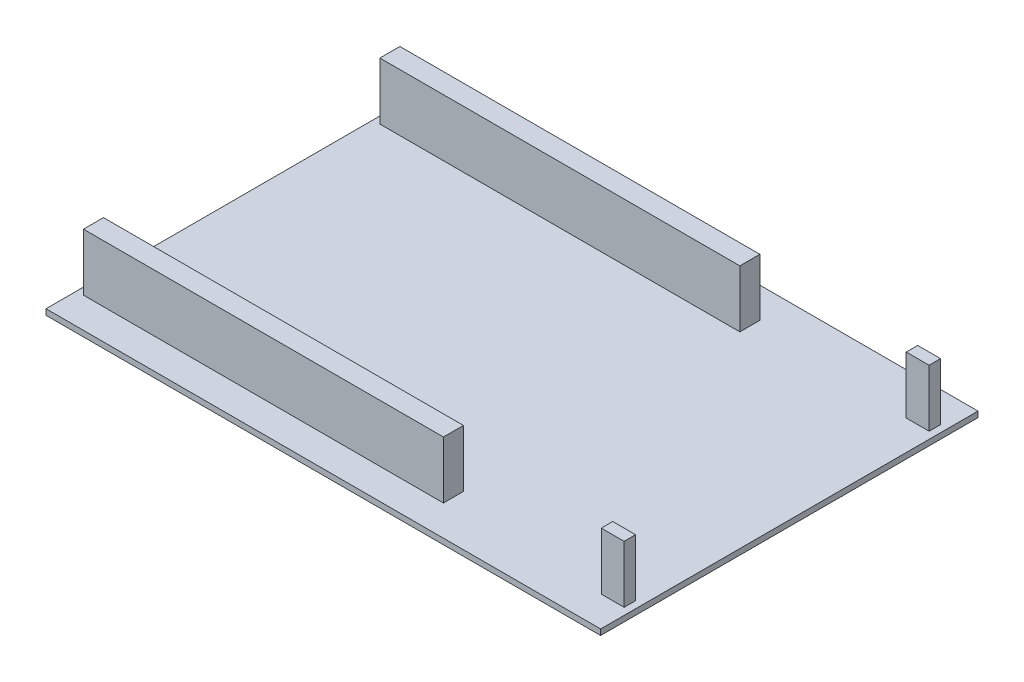
SolidWorks part; units mm, degrees
ref_plane "Front Plane" through (0, 0, 0) normal (0, 0, 1) x (1, 0, 0)
ref_plane "Top Plane" through (0, 0, 0) normal (0, 1, 0) x (1, 0, 0)
ref_plane "Right Plane" through (0, 0, 0) normal (1, 0, 0) x (0, 0, -1)
sketch "Sketch2" plane through (0, 0, 0) normal (0, 1, 0) x (1, 0, 0)
  line L1 (-48.5, -33) -> (48.5, -33)
  line L2 (-48.5, -33) -> (-48.5, 33)
  line L3 (-48.5, 33) -> (48.5, 33)
  line L4 (48.5, -33) -> (48.5, 33)
  line L5 (-48.5, -33) -> (48.5, 33) construction
  line L6 (-48.5, 33) -> (48.5, -33) construction
  point P0 (0, 0)
  dimension "D1" = 97
  dimension "D2" = 66
extrude "Boss-Extrude2" add sketch "Sketch2" along normal blind 1
sketch "Sketch3" plane through (0, 1, 0) normal (0, 1, 0) x (1, 0, 0)
  line L0 (-48.5, 33) -> (-48.5, -33) construction
  line L1 (15.68, 24.17) -> (-47.28, 24.17)
  line L2 (15.68, 24.17) -> (15.68, 27.67)
  line L3 (15.68, 27.67) -> (-47.28, 27.67)
  line L4 (-47.28, 24.17) -> (-47.28, 27.67)
  line L5 (15.68, 24.17) -> (-47.28, 27.67) construction
  line L6 (15.68, 27.67) -> (-47.28, 24.17) construction
  line L7 (48.5, 33) -> (-48.5, 33) construction
  line L8 (64.929, 0) -> (-72.8326, 0) construction
  line L9 (15.68, -27.67) -> (-47.28, -24.17) construction
  line L10 (15.68, -24.17) -> (-47.28, -27.67) construction
  line L11 (-47.28, -24.17) -> (-47.28, -27.67)
  line L12 (15.68, -27.67) -> (-47.28, -27.67)
  line L13 (15.68, -24.17) -> (15.68, -27.67)
  line L14 (15.68, -24.17) -> (-47.28, -24.17)
  point P0 (-15.8, 25.92)
  point P16 (-15.8, -25.92)
  dimension "D1" = 1.22
  dimension "D2" = 5.33
  dimension "D3" = 62.96
  dimension "D4" = 3.5
extrude "Boss-Extrude3" add sketch "Sketch3" along normal blind 10
sketch "Sketch4" plane through (0, 0, 0) normal (0, -1, 0) x (1, 0, 0)
  line L0 (-48.5, 33) -> (48.5, 33) construction
  line L1 (-51.5, 14.34) -> (-42.5, 14.34)
  line L2 (-51.5, 14.34) -> (-51.5, 20.34)
  line L3 (-51.5, 20.34) -> (-42.5, 20.34)
  line L4 (-42.5, 14.34) -> (-42.5, 20.34)
  line L5 (-51.5, 14.34) -> (-42.5, 20.34) construction
  line L6 (-51.5, 20.34) -> (-42.5, 14.34) construction
  line L7 (-48.5, -33) -> (-48.5, 33) construction
  point P0 (-47, 17.34)
  dimension "D1" = 12.66
  dimension "D2" = 3
  dimension "D3" = 9
  dimension "D4" = 6
extrude "Boss-Extrude4" add sketch "Sketch4" along normal blind 10
sketch "Sketch5" plane through (0, 1, 0) normal (0, 1, 0) x (1, 0, 0)
  line L0 (48.5, 33) -> (-48.5, 33) construction
  line L1 (47.28, 27.67) -> (43.28, 27.67)
  line L2 (47.28, 27.67) -> (47.28, 25.67)
  line L3 (47.28, 25.67) -> (43.28, 25.67)
  line L4 (43.28, 27.67) -> (43.28, 25.67)
  line L5 (47.28, 27.67) -> (43.28, 25.67) construction
  line L6 (47.28, 25.67) -> (43.28, 27.67) construction
  line L7 (48.5, -33) -> (48.5, 33) construction
  line L8 (62.0823, 0) -> (-62.7474, 0) construction
  line L9 (47.28, -25.67) -> (43.28, -27.67) construction
  line L10 (47.28, -27.67) -> (43.28, -25.67) construction
  line L11 (43.28, -27.67) -> (43.28, -25.67)
  line L12 (47.28, -25.67) -> (43.28, -25.67)
  line L13 (47.28, -27.67) -> (47.28, -25.67)
  line L14 (47.28, -27.67) -> (43.28, -27.67)
  point P0 (45.28, 26.67)
  point P16 (45.28, -26.67)
  dimension "D1" = 5.33
  dimension "D2" = 1.22
  dimension "D3" = 4
  dimension "D4" = 2
extrude "Boss-Extrude5" add sketch "Sketch5" along normal blind 10
